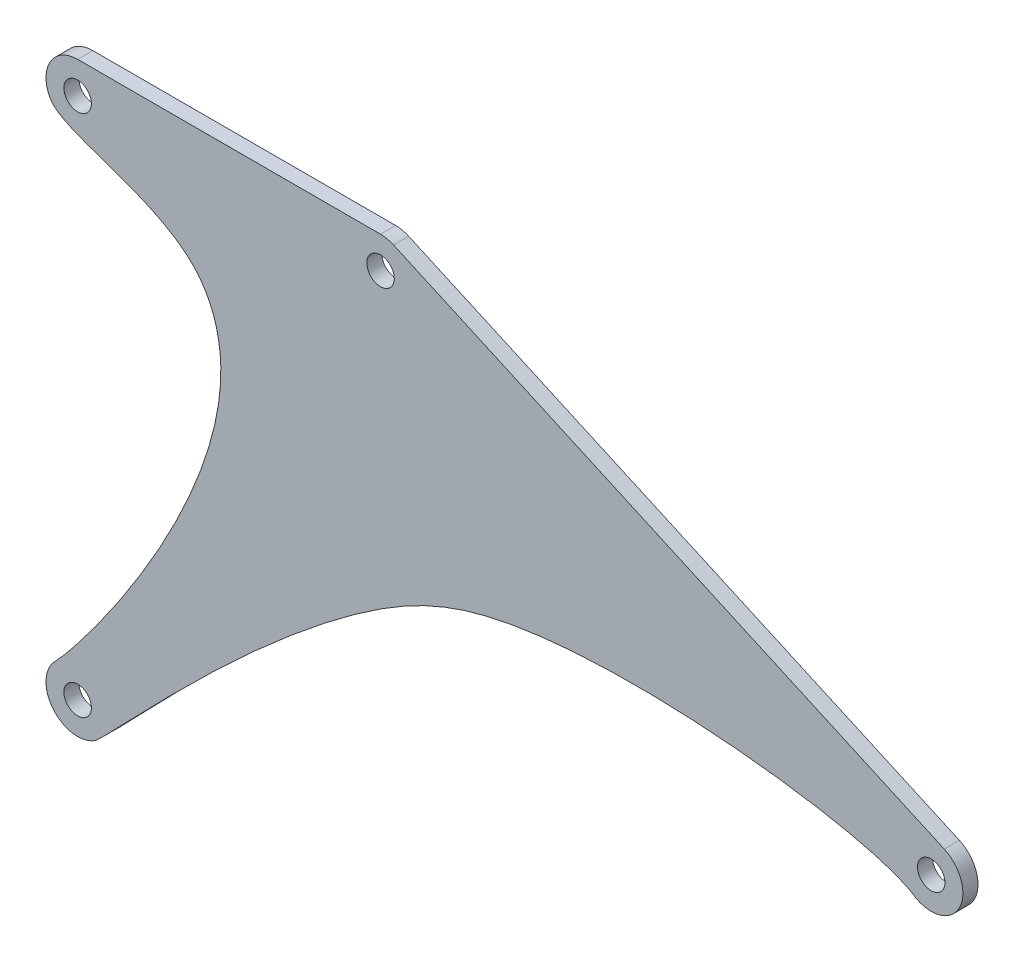
SolidWorks part; units mm, degrees
material "1.0490 (S275N)"
ref_plane "Front Plane" through (0, 0, 0) normal (0, 0, 1) x (1, 0, 0)
ref_plane "Top Plane" through (0, 0, 0) normal (0, 1, 0) x (1, 0, 0)
ref_plane "Right Plane" through (0, 0, 0) normal (1, 0, 0) x (0, 0, -1)
sketch "Sketch1" plane through (0, 0, 0) normal (0, 0, 1) x (1, 0, 0)
  line L0 (-110, 11.5) -> (0, 11.5)
  line L1 (4.7192, 10.4871) -> (204.7192, -79.5129)
  circle A0 centre (0, 0) radius 5
  circle A2 centre (200, -90) radius 5
  circle A4 centre (-110, -190) radius 5
  circle A5 centre (-110, 0) radius 5
  arc A6 (-110, 11.5) -> (-119.9148, -5.8263) centre (-110, 0) ccw
  arc A7 (-118.2653, -182.0041) -> (-103.6052, -199.558) centre (-110, -190) ccw
  arc A8 (193.5353, -99.5109) -> (204.7192, -79.5129) centre (200, -90) ccw
  arc A9 (4.7192, 10.4871) -> (0, 11.5) centre (0, 0) ccw
  spline S0 degree 3 poles (-119.9148, -5.8263) (-114.935, -14.3007) (-66.4482, -18.6928) (-46.8137, -89.4069) (-106.0836, -169.412) (-118.2653, -182.0041) knots 0 0 0 0 0.300299 0.455611 1 1 1 1
  spline S1 degree 3 poles (-103.6052, -199.558) (-99.1666, -196.5884) (-37.7478, -126.0459) (58.8347, -72.841) (177.3788, -88.5292) (193.5353, -99.5109) knots 0 0 0 0 0.472274 0.598363 1 1 1 1
  dimension "D1" = 10
  dimension "D2" = 10
  dimension "D3" = 10
  dimension "D4" = 10
  dimension "D10" = 23
  dimension "D11" = 23
  dimension "D12" = 23
  dimension "D13" = 23
  dimension "D5" = 110
  dimension "D6" = 200
  dimension "D7" = 90
  dimension "D8" = 190
extrude "link_BCEF" add sketch "Sketch1" along normal mid plane 5.5
